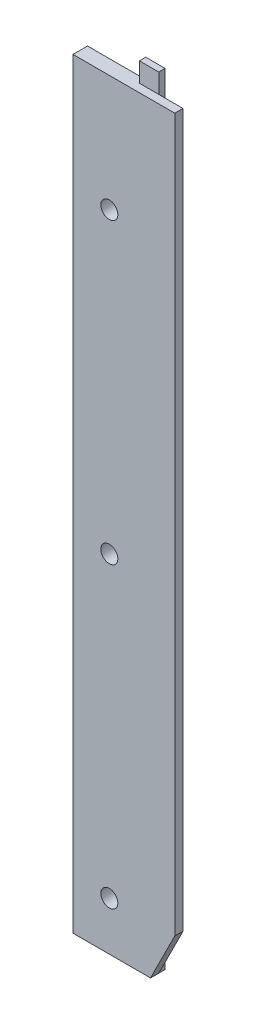
SolidWorks part; units mm, degrees
ref_plane "Front Plane" through (0, 0, 0) normal (0, 0, 1) x (1, 0, 0)
ref_plane "Top Plane" through (0, 0, 0) normal (0, 1, 0) x (1, 0, 0)
ref_plane "Right Plane" through (0, 0, 0) normal (1, 0, 0) x (0, 0, -1)
sketch "Sketch1" plane through (0, 0, 0) normal (0, 0, 1) x (1, 0, 0)
  line L1 (-10.5, -78.5) -> (10.5, -78.5)
  line L2 (-10.5, -78.5) -> (-10.5, 78.5)
  line L3 (-10.5, 78.5) -> (10.5, 78.5)
  line L4 (10.5, -78.5) -> (10.5, 78.5)
  line L5 (-10.5, -78.5) -> (10.5, 78.5) construction
  line L6 (-10.5, 78.5) -> (10.5, -78.5) construction
  point P0 (0, 0)
  dimension "D1" = 157
  dimension "D2" = 21
extrude "Boss-Extrude1" add sketch "Sketch1" along normal blind 1.7
sketch "Sketch2" plane through (0, 0, 0) normal (0, 0, -1) x (-1, 0, 0)
  line L0 (-5.5, 78.5) -> (-5.5, -78.5)
  line L4 (-10.5, 78.5) -> (-10.5, -78.5)
  line L5 (-10.5, -78.5) -> (10.5, -78.5)
  line L6 (10.5, -78.5) -> (10.5, 78.5)
  line L7 (10.5, 78.5) -> (-10.5, 78.5)
  line L9 (-5.5, -78.5) -> (10.5, -78.5)
  line L10 (10.5, -78.5) -> (10.5, 78.5)
  line L11 (10.5, 78.5) -> (-1.5, 78.5)
  line L12 (-5.5, 78.5) -> (-5.5, 82.5)
  line L13 (-5.5, 82.5) -> (-1.5, 82.5)
  line L14 (-1.5, 82.5) -> (-1.5, 78.5)
  line L15 (-10.5, 78.5) -> (10.5, 78.5) construction
  point P6 (-0.9057, 78.5)
  point P9 (0, 0)
  point P13 (-5.5, 75.9427)
  point P14 (0, 0)
  point P15 (-5.5, 82.5808)
  point P16 (-5.5, 78.5)
  dimension "D2" = 16
  dimension "D3" = 4
  dimension "D1" = 0
extrude "Boss-Extrude2" add sketch "Sketch2" along normal blind 1.3
sketch "Sketch3" plane through (0, 0, 1.7) normal (0, 0, 1) x (1, 0, 0)
  line L0 (-10.5, 78.5) -> (-10.5, -78.5) construction
  line L1 (10.5, 78.5) -> (-10.5, 78.5) construction
  circle A0 centre (-3, 54.5) radius 1.75
  circle A1 centre (-3, -7) radius 1.75
  circle A2 centre (-3, -68.5) radius 1.75
  point P10 (0, 0)
  point P11 (0, 0)
  dimension "D1" = 3.5
  dimension "D2" = 7.5
  dimension "D3" = 24
  dimension "D5" = 61.5
  dimension "D4" = 61.5
extrude "Cut-Extrude1" cut sketch "Sketch3" against normal through all
sketch "Sketch4" plane through (0, 0, 1.7) normal (0, 0, 1) x (1, 0, 0)
  line L0 (5.4993, -78.5) -> (10.5, -68.5007)
  line L1 (-10.5, -78.5) -> (10.5, -78.5) construction
  line L2 (10.5, -78.5) -> (10.5, 78.5) construction
  line L3 (5.4993, -78.5) -> (10.5, -78.5)
  line L4 (10.5, -78.5) -> (10.5, -68.5007)
  dimension "D1" = 11.18
  dimension "D2" = 116.57
extrude "Cut-Extrude2" cut sketch "Sketch4" against normal through all and the other way through all
